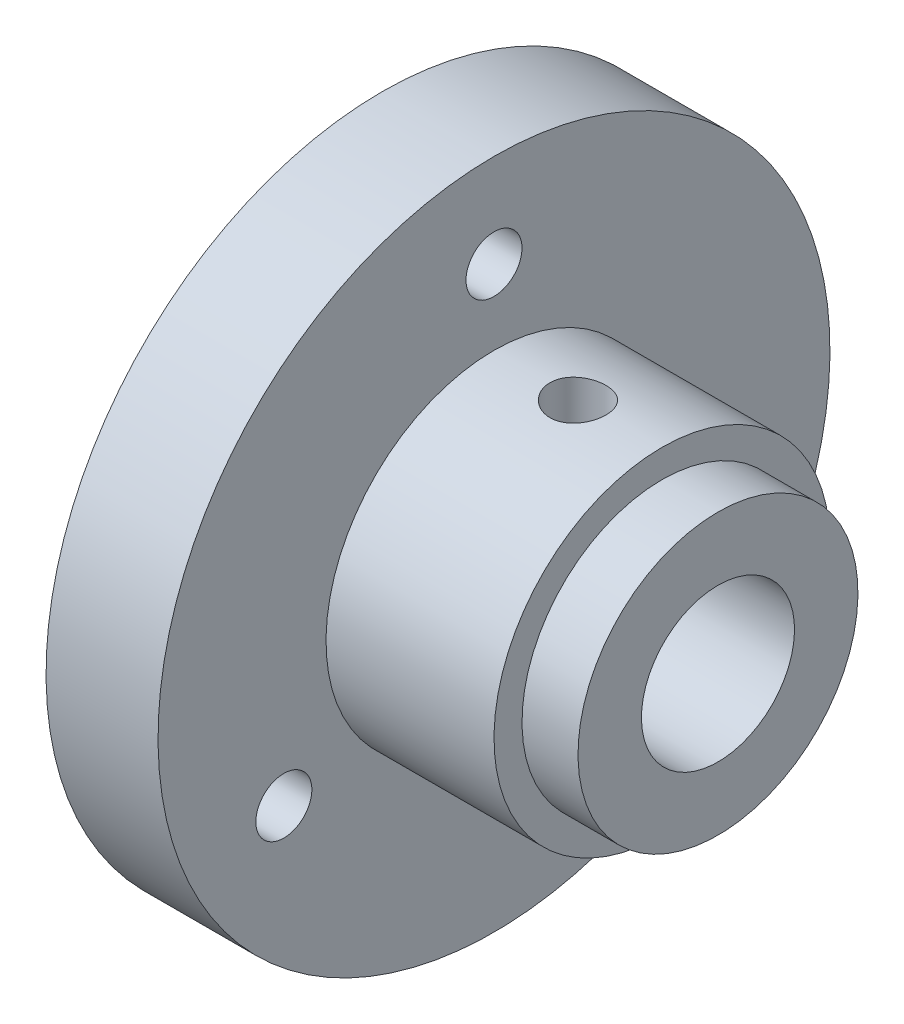
SolidWorks part; units mm, degrees
ref_plane "Plan de face" through (0, 0, 0) normal (0, 0, 1) x (1, 0, 0)
ref_plane "Plan de dessus" through (0, 0, 0) normal (0, 1, 0) x (1, 0, 0)
ref_plane "Plan de droite" through (0, 0, 0) normal (1, 0, 0) x (0, 0, -1)
sketch "Esquisse1" plane through (0, 0, 0) normal (0, 0, 1) x (1, 0, 0)
  line L0 (0, 0) -> (-18, 0) construction
  line L1 (0, 4.1) -> (-18, 4.1)
  line L3 (-3, 9) -> (-12, 9)
  line L7 (-12, 18) -> (-18, 18)
  line L8 (-18, 4.1) -> (-18, 18)
  line L9 (-18, 4.1) -> (-18, 0) construction
  line L10 (-3, 9) -> (-3, 7.5)
  line L11 (-12, 18) -> (-12, 9)
  line L14 (-3, 7.5) -> (0, 7.5)
  line L15 (0, 4.1) -> (0, 7.5)
  line L16 (0, 4.1) -> (0, 0) construction
  point P0 (-12, 9)
  dimension "D1" = 4.1
  dimension "D2" = 18
  dimension "D3" = 6
  dimension "D4" = 9
  dimension "D5" = 9
  dimension "D6" = 7.5
  dimension "D7" = 3
revolve "Révolution1" add sketch "Esquisse1" angle 360 about L0
sketch "Esquisse2" plane through (-12, 0, 0) normal (1, 0, 0) x (0, 0, -1)
  line L0 (0, 13) -> (0, 0) construction
  circle A0 centre (0, 13) radius 1.5
  circle A1 centre (11.2583, -6.5) radius 1.5
  circle A2 centre (-11.2583, -6.5) radius 1.5
  point P11 (0, 0)
  dimension "D1" = 3
  dimension "D2" = 13
  dimension "D3" = 3
extrude "Enlèv. mat.-Extru.1" cut sketch "Esquisse2" against normal through all
ref_plane "Plan2" through (0, 9, 0) normal (0, 1, 0) x (1, 0, 0)
sketch "Esquisse3" plane through (0, 9, 0) normal (0, 1, 0) x (1, 0, 0)
  line L0 (-3, 0) -> (-12, 0) construction
  line L1 (-12, -1.5) -> (-12, 1.5) construction
  line L2 (-3, -7.5) -> (-3, 7.5) construction
  circle A0 centre (-7.5, 0) radius 1.5
  point P8 (-7.5, 0)
  dimension "D1" = 3
extrude "Enlèv. mat.-Extru.2" cut sketch "Esquisse3" against normal up to next
